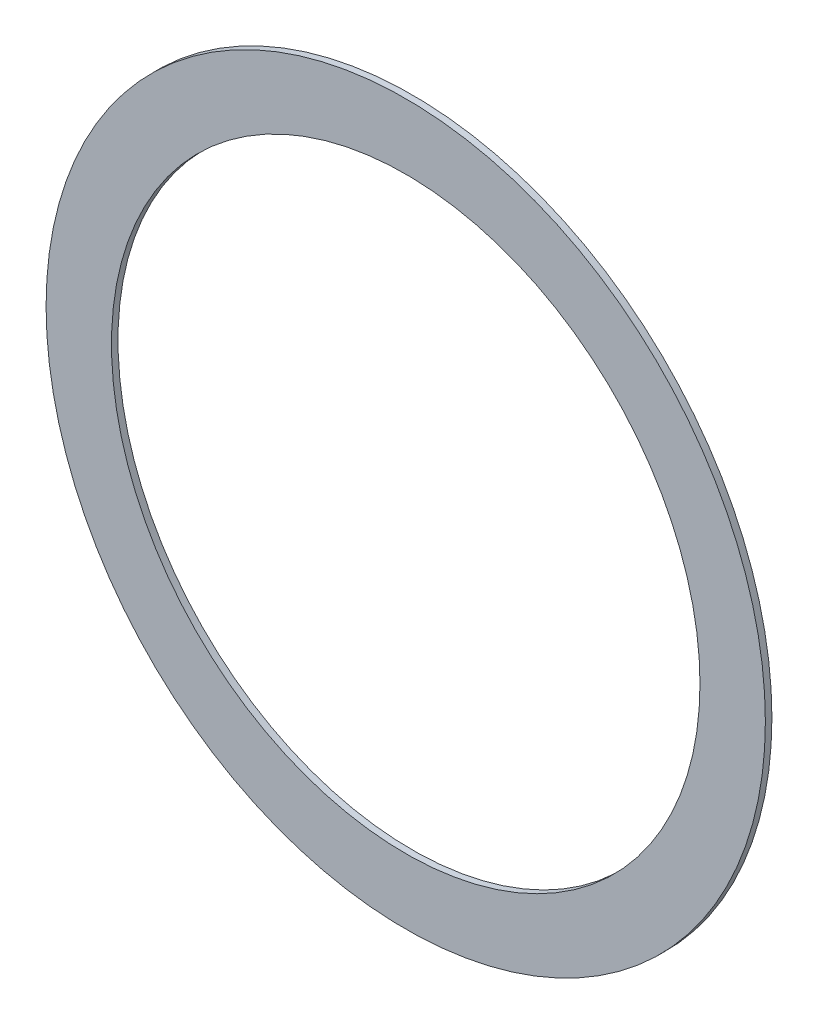
SolidWorks part; units mm, degrees
ref_plane "Front Plane" through (0, 0, 0) normal (0, 0, 1) x (1, 0, 0)
ref_plane "Top Plane" through (0, 0, 0) normal (0, 1, 0) x (1, 0, 0)
ref_plane "Right Plane" through (0, 0, 0) normal (1, 0, 0) x (0, 0, -1)
sketch "Sketch1" plane through (0, 0, 0) normal (0, 0, 1) x (1, 0, 0)
  circle A0 centre (0, 0) radius 2.25
  circle A1 centre (0, 0) radius 2.75
extrude "Boss-Extrude1" add sketch "Sketch1" along normal blind 0.05
